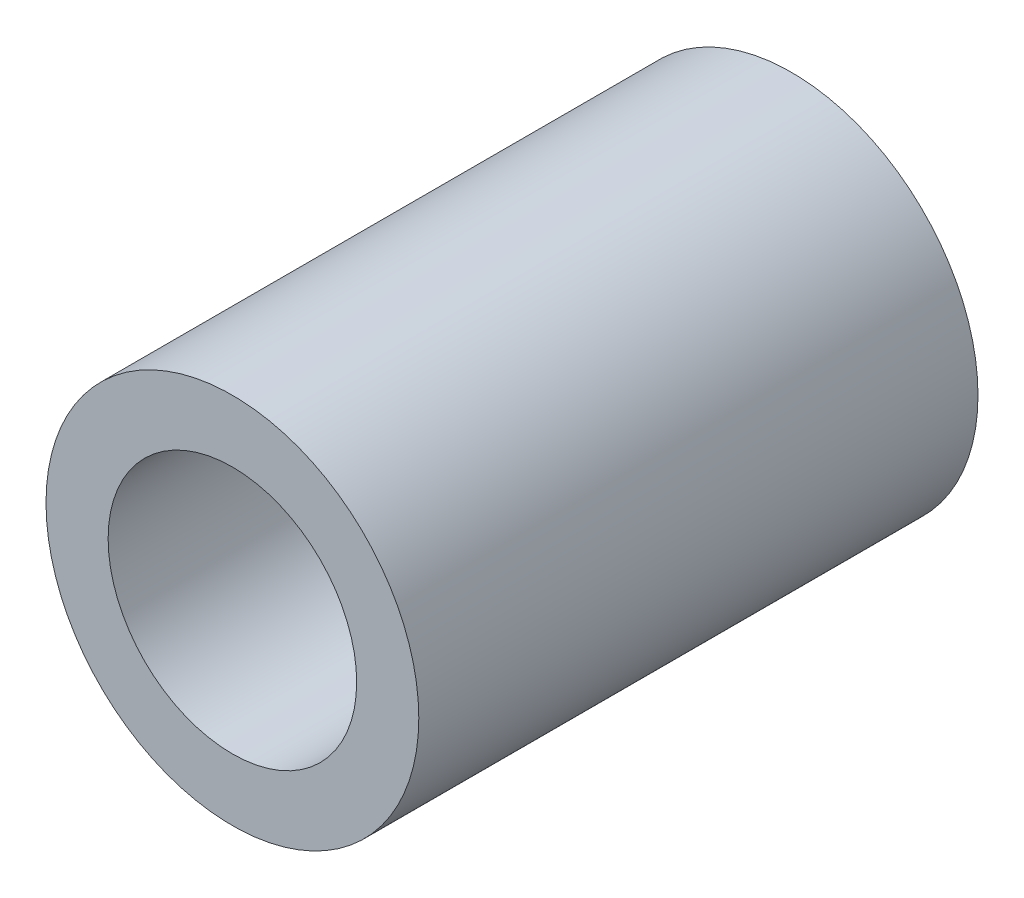
SolidWorks part; units mm, degrees
ref_plane "Front Plane" through (0, 0, 0) normal (0, 0, 1) x (1, 0, 0)
ref_plane "Top Plane" through (0, 0, 0) normal (0, 1, 0) x (1, 0, 0)
ref_plane "Right Plane" through (0, 0, 0) normal (1, 0, 0) x (0, 0, -1)
sketch "Sketch1" plane through (0, 0, 0) normal (0, 0, 1) x (1, 0, 0)
  circle A0 centre (0, 0) radius 3
  circle A1 centre (0, 0) radius 2
  dimension "D1" = 6
  dimension "D2" = 4
extrude "Boss-Extrude1" add sketch "Sketch1" along normal blind 9
equation "\"OD\"= 6.0mm"
equation "\"ID\"= 4.0mm"
equation "\"Height\" = 9mm"
equation "\"D1@Sketch1\"=\"OD\""
equation "\"D2@Sketch1\"=\"ID\""
equation "\"D1@Boss-Extrude1\"=\"Height\""
